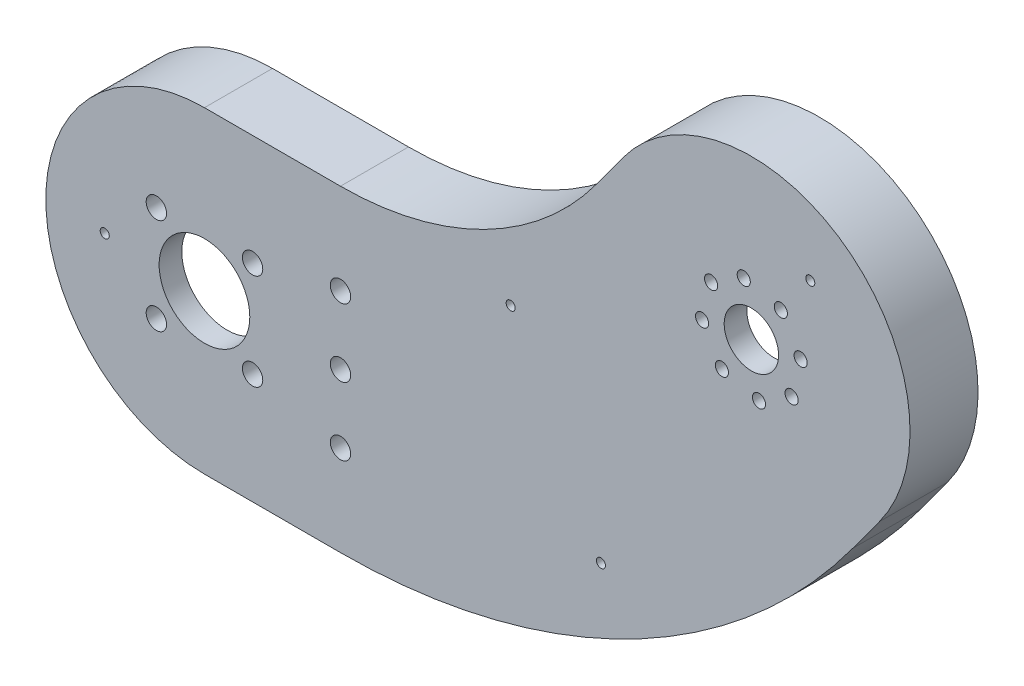
SolidWorks part; units mm, degrees
ref_plane "정면" through (0, 0, 0) normal (0, 0, 1) x (1, 0, 0)
ref_plane "윗면" through (0, 0, 0) normal (0, 1, 0) x (1, 0, 0)
ref_plane "우측면" through (0, 0, 0) normal (1, 0, 0) x (0, 0, -1)
sketch "스케치1" plane through (0, 0, 0) normal (0, 0, 1) x (1, 0, 0)
  line L0 (0, 35) -> (30, 35)
  line L1 (0, -35) -> (30, -35)
  line L2 (30, -965) -> (30, 49035) construction
  line L4 (86.4793, 63.6467) -> (92.3869, 71.7152)
  line L6 (148.8662, 30.362) -> (142.9585, 22.2935)
  arc A0 (0, 35) -> (0, -35) centre (0, 0) ccw
  arc A1 (30, 35) -> (86.4793, 63.6467) centre (30, 105) ccw
  arc A2 (30, -35) -> (142.9585, 22.2935) centre (30, 105) ccw
  arc A3 (148.8662, 30.362) -> (92.3869, 71.7152) centre (120.6265, 51.0386) ccw
  point P1 (30, 105)
  dimension "D1" = 70
  dimension "D5" = 140
  dimension "D6" = 280
  dimension "D7" = 70
  dimension "D2" = 30
  dimension "D3" = 30
  dimension "D4" = 70
  dimension "D8" = 10
extrude "보스-돌출1" add sketch "스케치1" along normal blind 20
chamfer "모따기1" distance 10 angle 45 8 edges at (-35, 0, 0) (15, -35, 0) (15, 35, 0) (93.3289, -19.8577, 0) (61.6644, 42.5711, 0) (145.9123, 26.3277, 0) (89.4331, 67.681, 0) (141.3031, 79.2782, 0)
sketch "스케치2" plane through (0, 0, 0) normal (0, 0, -1) x (-1, 0, 0)
  line L8 (-30, -25) -> (0, -25)
  line L9 (0, 25) -> (-30, 25)
  line L10 (-94.5477, 57.7391) -> (-100.4553, 65.8076)
  line L11 (-140.7977, 36.2696) -> (-134.8901, 28.2011)
  line L12 (-30, -25) -> (0, -25)
  line L13 (0, 25) -> (-30, 25)
  line L14 (-94.5477, 57.7391) -> (-100.4553, 65.8076)
  line L15 (-140.7977, 36.2696) -> (-134.8901, 28.2011)
  arc A8 (0, -25) -> (0, 25) centre (0, 0) ccw
  arc A9 (-94.5477, 57.7391) -> (-30, 25) centre (-30, 105) ccw
  arc A10 (-100.4553, 65.8076) -> (-140.7977, 36.2696) centre (-120.6265, 51.0386) ccw
  arc A11 (-134.8901, 28.2011) -> (-30, -25) centre (-30, 105) ccw
  arc A12 (0, -25) -> (0, 25) centre (0, 0) ccw
  arc A13 (-94.5477, 57.7391) -> (-30, 25) centre (-30, 105) ccw
  arc A14 (-100.4553, 65.8076) -> (-140.7977, 36.2696) centre (-120.6265, 51.0386) ccw
  arc A15 (-134.8901, 28.2011) -> (-30, -25) centre (-30, 105) ccw
  dimension "D1" = 0
extrude "컷-돌출1" cut sketch "스케치2" against normal blind 15
sketch "스케치3" plane through (0, 0, 20) normal (0, 0, 1) x (1, 0, 0)
  line L0 (148.8662, 30.362) -> (76.1824, 83.5799) construction
  line L1 (88.8891, 7.6924) -> (29626.9295, 40350.0296) construction
  line L2 (120.6265, 51.0386) -> (49533.5154, 7690.8301) construction
  line L3 (120.5409, 51.5921) -> (-7519.2506, 49464.4809) construction
  circle A0 centre (120.6265, 51.0386) radius 15 construction
  circle A1 centre (127.1249, 59.9139) radius 1.45
  circle A2 centre (129.5018, 44.5402) radius 1.45
  circle A3 centre (114.1281, 42.1633) radius 1.45
  circle A4 centre (111.7512, 57.537) radius 1.45
  circle A5 centre (120.6265, 51.0386) radius 6
  circle A6 centre (118.9458, 61.9094) radius 1.45
  circle A7 centre (131.4974, 52.7193) radius 1.45
  circle A8 centre (122.3073, 40.1677) radius 1.45
  circle A9 centre (109.7557, 49.3578) radius 1.45
  point P2 (92.3869, 71.7152)
  dimension "D1" = 30
  dimension "D3" = 2.9
  dimension "D5" = 2.9
  dimension "D6" = 2.9
  dimension "D7" = 2.9
  dimension "D11" = 12
  dimension "D14" = 2.9
  dimension "D15" = 2.9
  dimension "D16" = 2.9
  dimension "D17" = 2.9
  dimension "D2" = 35
  dimension "D4" = 11
  dimension "D8" = 11
  dimension "D9" = 11
  dimension "D10" = 11
  dimension "D12" = 45
  dimension "D13" = 45
  dimension "D18" = 11
  dimension "D19" = 11
  dimension "D20" = 11
  dimension "D21" = 11
sketch "스케치4" plane through (0, 0, 20) normal (0, 0, 1) x (1, 0, 0)
  line L0 (0, 28.2577) -> (0, -20.5587) construction
  line L1 (0, 0) -> (-35355.3391, 35355.3391) construction
  line L2 (0, 0) -> (-50000, 0) construction
  line L3 (30, 0) -> (30, 50000) construction
  line L4 (0.3232, 0.3232) -> (35355.6623, 35355.6623) construction
  circle A0 centre (0, 0) radius 10
  circle A1 centre (10.6066, 10.6066) radius 2.25
  circle A2 centre (-10.6066, -10.6066) radius 2.25
  circle A3 centre (10.6066, -10.6066) radius 2.25
  circle A4 centre (-10.6066, 10.6066) radius 2.25
  circle A5 centre (30, 0) radius 2.25
  circle A6 centre (30, 15) radius 2.25
  circle A7 centre (30, -15) radius 2.25
  circle A8 centre (0, 0) radius 15 construction
  point P20 (0, 35)
  dimension "D1" = 20
  dimension "D2" = 4.5
  dimension "D3" = 4.5
  dimension "D4" = 4.5
  dimension "D5" = 4.5
  dimension "D6" = 4.5
  dimension "D7" = 4.5
  dimension "D8" = 4.5
  dimension "D17" = 30
  dimension "D9" = 35
  dimension "D14" = 30
  dimension "D15" = 15
  dimension "D16" = 15
extrude "컷-돌출3" cut sketch "스케치4" against normal up to next
sketch "스케치5" plane through (0, 0, 15) normal (0, 0, -1) x (-1, 0, 0)
  line L0 (-30, 27.6131) -> (-30, 50027.6131) construction
  line L2 (-91.433, 60.0197) -> (40250.9042, 29598.06) construction
  line L4 (-61.6644, 42.5711) -> (22555.7844, 44634.6221) construction
  line L5 (0, 0) -> (50000, 0) construction
  line L6 (-120.6265, 51.0386) -> (29417.4138, -40291.2986) construction
  arc A0 (-86.4793, 63.6467) -> (-30, 35) centre (-30, 105) ccw construction
  circle A1 centre (-87.4483, -8.2638) radius 4
  circle A2 centre (22, 0) radius 4
  circle A3 centre (-67.545, 30.9772) radius 4
  circle A4 centre (-133.6233, 68.7892) radius 4
  arc A5 (0, -25) -> (0, 25) centre (0, 0) ccw construction
  arc A6 (-94.5477, 57.7391) -> (-30, 25) centre (-30, 105) ccw construction
  arc A7 (-134.8901, 28.2011) -> (-30, -25) centre (-30, 105) ccw construction
  arc A8 (-100.4553, 65.8076) -> (-140.7977, 36.2696) centre (-120.6265, 51.0386) ccw construction
  point P9 (-61.6644, 42.5711)
  point P25 (-66.1879, 33.6527)
  point P26 (-88.8054, -10.9393)
  point P29 (25, 0)
  point P34 (-135.3955, 71.2098)
  point P38 (-83.2568, 0)
  dimension "D1" = 8
  dimension "D2" = 8
  dimension "D3" = 8
  dimension "D4" = 8
  dimension "D5" = 3
  dimension "D6" = 3
  dimension "D7" = 3
  dimension "D8" = 3
extrude "보스-돌출2" add sketch "스케치5" along normal blind 5
fillet "필렛1" radius 5 8 edges at (86.4057, -12.1255, 12.5) (91.1801, -9.704, 12.5) (-24.8409, 2.8159, 12.5) (-24.8409, -2.8159, 12.5) (63.8526, 32.5155, 12.5) (68.4851, 34.8651, 12.5) (137.5735, 69.4179, 12.5) (133.0296, 72.7449, 12.5)
sketch "스케치6" plane through (0, 0, 10) normal (0, 0, -1) x (-1, 0, 0)
  line L0 (-144.8319, 33.3158) -> (40197.5053, 29571.3561) construction
  line L1 (-140.7977, 36.2696) -> (-148.8662, 30.362) construction
  line L2 (-120.6265, 51.0386) -> (-29658.6669, 40393.3758) construction
  line L3 (-30, 27.1175) -> (-30, 50027.1175) construction
  line L5 (-30, 0) -> (49970, 0) construction
  line L7 (-88.0978, 62.4617) -> (40254.2394, 29600.5021) construction
  line L8 (-66.1879, 33.6527) -> (22551.2609, 44625.7037) construction
  line L9 (-133.6233, 68.7892) -> (40208.714, 29606.8296) construction
  line L10 (-67.545, 30.9772) -> (44524.506, -22586.4716) construction
  line L11 (-87.4483, -8.2638) -> (44504.6026, -22625.7126) construction
  line L12 (22, 0) -> (22, 50000) construction
  circle A0 centre (-87.4483, -8.2638) radius 1
  circle A1 centre (22, 0) radius 1
  circle A2 centre (-67.545, 30.9772) radius 1
  circle A3 centre (-133.6233, 68.7892) radius 1
  arc A4 (-94.5477, 57.7391) -> (-30, 25) centre (-30, 105) ccw construction
  point P12 (-144.8319, 33.3158)
  point P28 (-66.1879, 33.6527)
  dimension "D1" = 2
  dimension "D2" = 2
  dimension "D3" = 2
  dimension "D4" = 2
extrude "컷-돌출4" cut sketch "스케치6" against normal up to next
fillet "필렛2" radius 5 8 edges at (145.9123, 26.3277, 10) (93.3289, -19.8577, 10) (15, -35, 10) (-35, 0, 10) (15, 35, 10) (61.6644, 42.5711, 10) (89.4331, 67.681, 10) (141.3031, 79.2782, 10)
extrude "컷-돌출5" cut sketch "스케치3" against normal up to next and the other way through all
ref_plane "평면1" through (0, 0, 0) normal (0, 0, 1) x (1, 0, 0)
sketch "스케치7" plane through (0, 0, 0) normal (0, 0, 1) x (1, 0, 0)
  line L20 (142.9585, 22.2935) -> (148.8662, 30.362)
  line L21 (0, -35) -> (30, -35)
  line L22 (30, 35) -> (0, 35)
  line L23 (92.3869, 71.7152) -> (86.4793, 63.6467)
  line L24 (142.9585, 22.2935) -> (148.8662, 30.362)
  line L25 (0, -35) -> (30, -35)
  line L26 (30, 35) -> (0, 35)
  line L27 (92.3869, 71.7152) -> (86.4793, 63.6467)
  line L72 (134.8901, 28.2011) -> (140.7977, 36.2696)
  line L73 (0, -25) -> (30, -25)
  line L74 (30, 25) -> (0, 25)
  line L75 (100.4553, 65.8076) -> (94.5477, 57.7391)
  line L76 (134.8901, 28.2011) -> (140.7977, 36.2696)
  line L77 (0, -25) -> (30, -25)
  line L78 (30, 25) -> (0, 25)
  line L79 (100.4553, 65.8076) -> (94.5477, 57.7391)
  arc A24 (30, -35) -> (142.9585, 22.2935) centre (30, 105) ccw
  arc A25 (0, 35) -> (0, -35) centre (0, 0) ccw
  arc A26 (30, 35) -> (86.4793, 63.6467) centre (30, 105) ccw
  arc A27 (148.8662, 30.362) -> (92.3869, 71.7152) centre (120.6265, 51.0386) ccw
  arc A28 (30, -35) -> (142.9585, 22.2935) centre (30, 105) ccw
  arc A29 (0, 35) -> (0, -35) centre (0, 0) ccw
  arc A30 (30, 35) -> (86.4793, 63.6467) centre (30, 105) ccw
  arc A31 (148.8662, 30.362) -> (92.3869, 71.7152) centre (120.6265, 51.0386) ccw
  arc A84 (30, -25) -> (134.8901, 28.2011) centre (30, 105) ccw
  arc A85 (0, 25) -> (0, -25) centre (0, 0) ccw
  arc A86 (30, 25) -> (94.5477, 57.7391) centre (30, 105) ccw
  arc A87 (140.7977, 36.2696) -> (100.4553, 65.8076) centre (120.6265, 51.0386) ccw
  arc A88 (30, -25) -> (134.8901, 28.2011) centre (30, 105) ccw
  arc A89 (0, 25) -> (0, -25) centre (0, 0) ccw
  arc A90 (30, 25) -> (94.5477, 57.7391) centre (30, 105) ccw
  arc A91 (140.7977, 36.2696) -> (100.4553, 65.8076) centre (120.6265, 51.0386) ccw
  dimension "D1" = 0
  dimension "D2" = 0
extrude "보스-돌출3" add sketch "스케치7" along normal blind 13
sketch "스케치8" plane through (0, 0, 0) normal (0, 0, -1) x (-1, 0, 0)
  line L8 (-148.8662, 30.362) -> (-142.9585, 22.2935)
  line L9 (-30, -35) -> (0, -35)
  line L10 (0, 35) -> (-30, 35)
  line L11 (-86.4793, 63.6467) -> (-92.3869, 71.7152)
  line L12 (-148.8662, 30.362) -> (-142.9585, 22.2935)
  line L13 (-30, -35) -> (0, -35)
  line L14 (0, 35) -> (-30, 35)
  line L15 (-86.4793, 63.6467) -> (-92.3869, 71.7152)
  line L32 (-140.7977, 36.2696) -> (-134.8901, 28.2011)
  line L33 (-30, -25) -> (0, -25)
  line L34 (0, 25) -> (-30, 25)
  line L35 (-94.5477, 57.7391) -> (-100.4553, 65.8076)
  line L36 (-140.7977, 36.2696) -> (-134.8901, 28.2011)
  line L37 (-30, -25) -> (0, -25)
  line L38 (0, 25) -> (-30, 25)
  line L39 (-94.5477, 57.7391) -> (-100.4553, 65.8076)
  arc A8 (-92.3869, 71.7152) -> (-148.8662, 30.362) centre (-120.6265, 51.0386) ccw
  arc A9 (-142.9585, 22.2935) -> (-30, -35) centre (-30, 105) ccw
  arc A10 (0, -35) -> (0, 35) centre (0, 0) ccw
  arc A11 (-86.4793, 63.6467) -> (-30, 35) centre (-30, 105) ccw
  arc A12 (-92.3869, 71.7152) -> (-148.8662, 30.362) centre (-120.6265, 51.0386) ccw
  arc A13 (-142.9585, 22.2935) -> (-30, -35) centre (-30, 105) ccw
  arc A14 (0, -35) -> (0, 35) centre (0, 0) ccw
  arc A15 (-86.4793, 63.6467) -> (-30, 35) centre (-30, 105) ccw
  arc A37 (-134.8901, 28.2011) -> (-30, -25) centre (-30, 105) ccw
  arc A38 (0, -25) -> (0, 25) centre (0, 0) ccw
  arc A39 (-94.5477, 57.7391) -> (-30, 25) centre (-30, 105) ccw
  arc A40 (-100.4553, 65.8076) -> (-140.7977, 36.2696) centre (-120.6265, 51.0386) ccw
  arc A41 (-134.8901, 28.2011) -> (-30, -25) centre (-30, 105) ccw
  arc A42 (0, -25) -> (0, 25) centre (0, 0) ccw
  arc A43 (-94.5477, 57.7391) -> (-30, 25) centre (-30, 105) ccw
  arc A44 (-100.4553, 65.8076) -> (-140.7977, 36.2696) centre (-120.6265, 51.0386) ccw
  dimension "D1" = 0
  dimension "D2" = 0
extrude "컷-돌출6" cut sketch "스케치8" against normal blind 5
